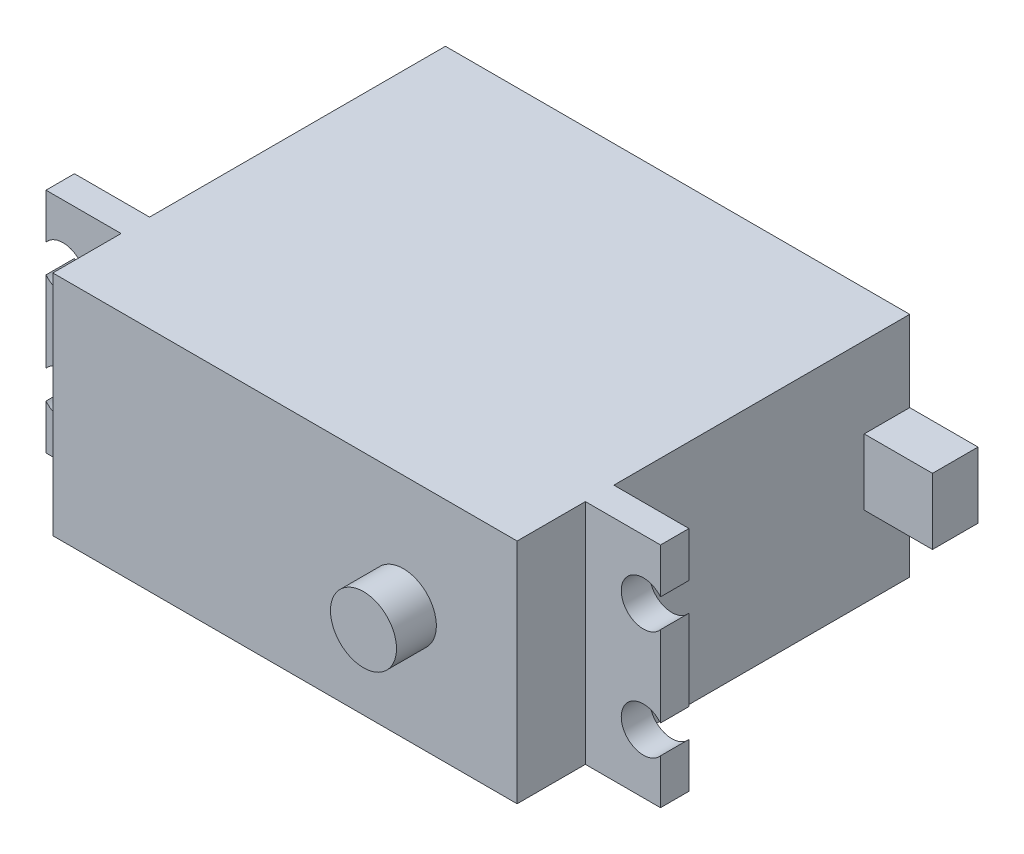
SolidWorks part; units mm, degrees
ref_plane "Front" through (0, 0, 0) normal (0, 0, 1) x (1, 0, 0)
ref_plane "Top" through (0, 0, 0) normal (0, 1, 0) x (1, 0, 0)
ref_plane "Right" through (0, 0, 0) normal (1, 0, 0) x (0, 0, -1)
sketch "Sketch1" plane through (0, 0, 0) normal (0, 0, 1) x (1, 0, 0)
  line L1 (-27, -10) -> (27, -10)
  line L2 (-27, -10) -> (-27, 10)
  line L3 (-27, 10) -> (27, 10)
  line L4 (27, -10) -> (27, 10)
  line L5 (-27, -10) -> (27, 10) construction
  line L6 (-27, 10) -> (27, -10) construction
  point P0 (0, 0)
  dimension "D1" = 54
  dimension "D2" = 20
extrude "Boss-Extrude1" add sketch "Sketch1" along normal blind 2.5
sketch "Sketch3" plane through (0, 0, 2.5) normal (0, 0, 1) x (1, 0, 0)
  line L0 (-27, 0) -> (27, 0) construction
  line L2 (-27, 10) -> (-27, -10) construction
  line L3 (27, -10) -> (27, 10) construction
  line L4 (0, 10) -> (0, -10) construction
  line L5 (27, 10) -> (-27, 10) construction
  line L6 (-27, -10) -> (27, -10) construction
  circle A0 centre (-25.5, 4.8) radius 1.95
  circle A1 centre (-25.5, -4.8) radius 1.95
  circle A2 centre (25.5, -4.8) radius 1.95
  circle A3 centre (25.5, 4.8) radius 1.95
  dimension "D1" = 3.9
  dimension "D2" = 4.8
  dimension "D3" = 1.5
extrude "Cut-Extrude1" cut sketch "Sketch3" against normal up to surface (2.5 mm away) up to face at (0, 0, 0)
sketch "Sketch4" plane through (0, 0, 2.5) normal (0, 0, 1) x (1, 0, 0)
  line L0 (27, 10) -> (-27, 10) construction
  line L1 (-20.4, -10) -> (20.4, -10)
  line L2 (-20.4, -10) -> (-20.4, 10)
  line L3 (-20.4, 10) -> (20.4, 10)
  line L4 (20.4, -10) -> (20.4, 10)
  line L5 (-20.4, -10) -> (20.4, 10) construction
  line L6 (-20.4, 10) -> (20.4, -10) construction
  line L7 (27, 6.046) -> (27, 10) construction
  point P0 (0, 0)
  dimension "D1" = 6.6
extrude "Boss-Extrude2" add sketch "Sketch4" along normal blind 6
sketch "Sketch5" plane through (0, 0, 0) normal (0, 0, -1) x (-1, 0, 0)
  line L0 (-27, 10) -> (27, 10) construction
  line L1 (-20.4, -10) -> (20.4, -10)
  line L2 (-20.4, -10) -> (-20.4, 10)
  line L3 (-20.4, 10) -> (20.4, 10)
  line L4 (20.4, -10) -> (20.4, 10)
  line L5 (-20.4, -10) -> (20.4, 10) construction
  line L6 (-20.4, 10) -> (20.4, -10) construction
  line L7 (-27, 6.046) -> (-27, 10) construction
  point P1 (0, 0)
  dimension "D1" = 6.6
extrude "Boss-Extrude3" add sketch "Sketch5" along normal blind 26
sketch "Sketch6" plane through (0, 0, 8.5) normal (0, 0, 1) x (1, 0, 0)
  line L0 (-20.4, 0) -> (20.4, 0) construction
  line L1 (-20.4, 10) -> (-20.4, -10) construction
  line L2 (20.4, -10) -> (20.4, 10) construction
  line L3 (20.4, -10) -> (20.4, 10) construction
  circle A0 centre (10.4, 0) radius 2.9
  dimension "D2" = 5.8
  dimension "D1" = 10
extrude "Boss-Extrude4" add sketch "Sketch6" along normal blind 3.5
sketch "Sketch7" plane through (20.4, 0, 0) normal (1, 0, 0) x (0, 0, -1)
  line L0 (26, 0) -> (0, 0) construction
  line L1 (26, 10) -> (26, -10) construction
  line L3 (22, 2.9) -> (26, 2.9)
  line L4 (22, 2.9) -> (22, -2.9)
  line L5 (22, -2.9) -> (26, -2.9)
  line L6 (26, 2.9) -> (26, -2.9)
  line L7 (22, 2.9) -> (26, -2.9) construction
  line L8 (22, -2.9) -> (26, 2.9) construction
  point P5 (24, 0)
  dimension "D1" = 5.8
  dimension "D2" = 4
extrude "Boss-Extrude5" add sketch "Sketch7" along normal blind 6
